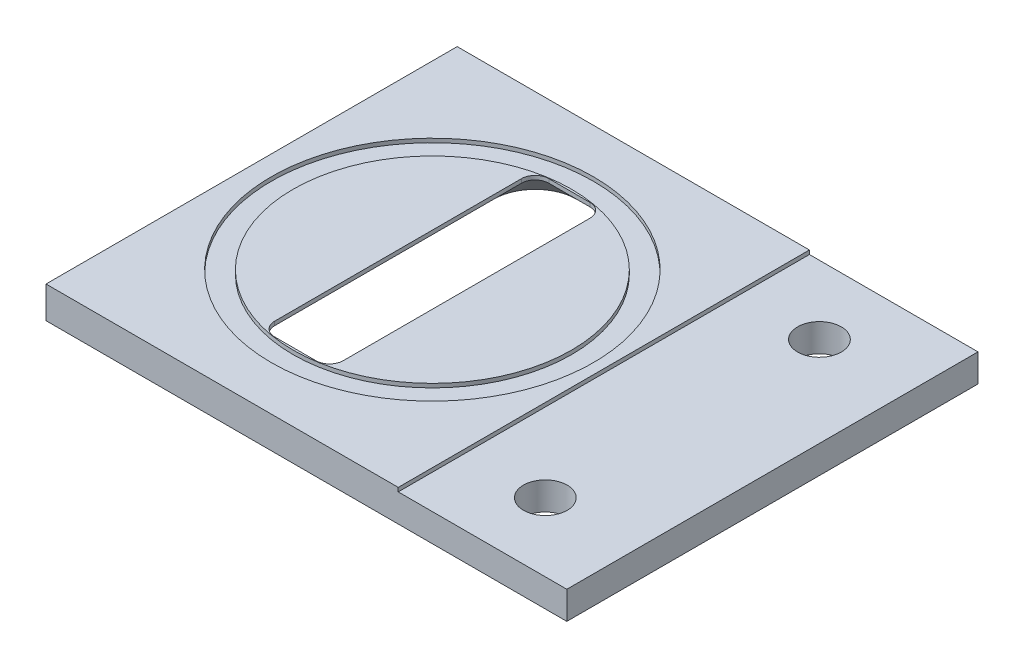
SolidWorks part; units mm, degrees
material "6061-T4 (SS)"
ref_plane "Front Plane" through (0, 0, 0) normal (0, 0, 1) x (1, 0, 0)
ref_plane "Top Plane" through (0, 0, 0) normal (0, 1, 0) x (1, 0, 0)
ref_plane "Right Plane" through (0, 0, 0) normal (1, 0, 0) x (0, 0, -1)
sketch "Sketch2" plane through (0, 0, 0) normal (0, 1, 0) x (1, 0, 0)
  line L5 (-13.189, 15) -> (24.811, 15)
  line L6 (-13.189, 15) -> (-13.189, -15)
  line L7 (-13.189, -15) -> (24.811, -15)
  line L8 (24.811, 15) -> (24.811, -15)
  line L9 (-13.189, 15) -> (24.811, -15) construction
  line L10 (-13.189, -15) -> (24.811, 15) construction
  dimension "D1" = 38
  dimension "D2" = 30
extrude "Boss-Extrude1" add sketch "Sketch2" along normal blind 2.032
sketch "Sketch4" plane through (0, 2.032, 0) normal (0, 1, 0) x (1, 0, 0)
  line L1 (1.5, -10) -> (-1.5, -10)
  line L2 (2.5, -9) -> (2.5, 9)
  line L3 (1.5, 10) -> (-1.5, 10)
  line L4 (-2.5, -9) -> (-2.5, 9)
  line L5 (2.5, -10) -> (-2.5, 10) construction
  line L6 (2.5, 10) -> (-2.5, -10) construction
  arc A0 (1.5, -10) -> (2.5, -9) centre (1.5, -9) ccw
  arc A1 (2.5, 9) -> (1.5, 10) centre (1.5, 9) ccw
  arc A2 (-1.5, 10) -> (-2.5, 9) centre (-1.5, 9) ccw
  arc A3 (-1.5, -10) -> (-2.5, -9) centre (-1.5, -9) cw
  point P0 (0, 0)
  dimension "D3" = 1
  dimension "D1" = 20
  dimension "D2" = 5
extrude "Cut-Extrude4" cut sketch "Sketch4" against normal through all draft 45 draft outward yes
sketch "Sketch5" plane through (0, 2.032, 0) normal (0, 1, 0) x (1, 0, 0)
  line L0 (18.2427, -15) -> (18.2427, 15) construction
  line L1 (-13.189, -15) -> (24.811, -15) construction
  line L2 (24.811, 15) -> (-13.189, 15) construction
  circle A0 centre (18.2427, -10) radius 1.595
  circle A1 centre (18.2427, 10) radius 1.595
  dimension "D3" = 3.19
  dimension "D4" = 3.19
  dimension "D1" = 5
  dimension "D2" = 5
extrude "Cut-Extrude5" cut sketch "Sketch5" against normal through all
sketch "Sketch6" plane through (0, 2.032, 0) normal (0, 1, 0) x (1, 0, 0)
  line L0 (0, 10.1625) -> (0, 11.75) construction
  line L1 (-13.189, -15) -> (12.511, -15)
  line L2 (-13.189, -15) -> (-13.189, 15)
  line L3 (-13.189, 15) -> (12.511, 15)
  line L4 (12.511, -15) -> (12.511, 15)
  line L5 (24.811, -15) -> (24.811, 15) construction
  line L6 (24.811, 15) -> (-13.189, 15) construction
  line L7 (0, -10) -> (1.5, -10)
  line L8 (-1.5, -10) -> (1.5, -10) construction
  line L9 (2.5, -9) -> (2.5, 9)
  line L10 (1.5, 10) -> (-1.5, 10)
  line L11 (-2.5, 9) -> (-2.5, -9)
  line L12 (-1.5, -10) -> (0, -10)
  line L13 (-2.5, 9) -> (-2.5, -9) construction
  line L14 (2.5, -9) -> (2.5, 9) construction
  line L15 (1.5, 10) -> (-1.5, 10) construction
  circle A0 centre (0, 0) radius 11.75
  circle A1 centre (0, 0) radius 10.1625
  circle A2 centre (0, 0) radius 11.75 construction
  arc A7 (-1.5, 10) -> (-2.5, 9) centre (-1.5, 9) ccw
  arc A8 (-1.5, 10) -> (-2.5, 9) centre (-1.5, 9) ccw construction
  arc A9 (2.5, 9) -> (1.5, 10) centre (1.5, 9) ccw
  arc A11 (2.5, 9) -> (1.5, 10) centre (1.5, 9) ccw construction
  arc A13 (-1.5, -10) -> (-2.5, -9) centre (-1.5, -9) cw
  arc A14 (-2.5, -9) -> (-1.5, -10) centre (-1.5, -9) ccw construction
  arc A15 (1.5, -10) -> (2.5, -9) centre (1.5, -9) ccw
  arc M1 (2.5, -9) -> (1.5, -10) centre (1.5, -9) cw
  line M2 (1.5, -10) -> (-1.5, -10)
  arc M3 (-1.5, -10) -> (-2.5, -9) centre (-1.5, -9) cw
  line M4 (-2.5, -9) -> (-2.5, 9)
  arc M5 (-2.5, 9) -> (-1.5, 10) centre (-1.5, 9) cw
  line M6 (-1.5, 10) -> (1.5, 10)
  arc M7 (1.5, 10) -> (2.5, 9) centre (1.5, 9) cw
  line M8 (2.5, 9) -> (2.5, -9)
  line M10 (24.811, 15) -> (-13.189, 15)
  line M11 (-13.189, 15) -> (-13.189, -15)
  line M12 (-13.189, -15) -> (24.811, -15)
  dimension "D1" = 1.5875
  dimension "D2" = 12.3
sketch "Sketch8" plane through (0, 2.032, 0) normal (0, 1, 0) x (1, 0, 0)
  line L0 (24.811, 15) -> (-13.189, 15) construction
  line L1 (-13.189, -15) -> (12.511, -15)
  line L2 (-13.189, -15) -> (-13.189, 15)
  line L3 (-13.189, 15) -> (12.511, 15)
  line L4 (12.511, -15) -> (12.511, 15)
  line L5 (24.811, -15) -> (24.811, 15) construction
  circle A0 centre (0, 0) radius 12.5
  circle A1 centre (0, 0) radius 12.5 construction
  dimension "D1" = 12.3
extrude "Boss-Extrude3" [suppressed] add sketch "Sketch8" along normal blind 2
extrude "Boss-Extrude4" add sketch "Sketch6" along normal blind 0.2874 contours L4 A0 M12 M10 M11 | A1 M8 M1 M2 M3 M4 M5 M6 M7
